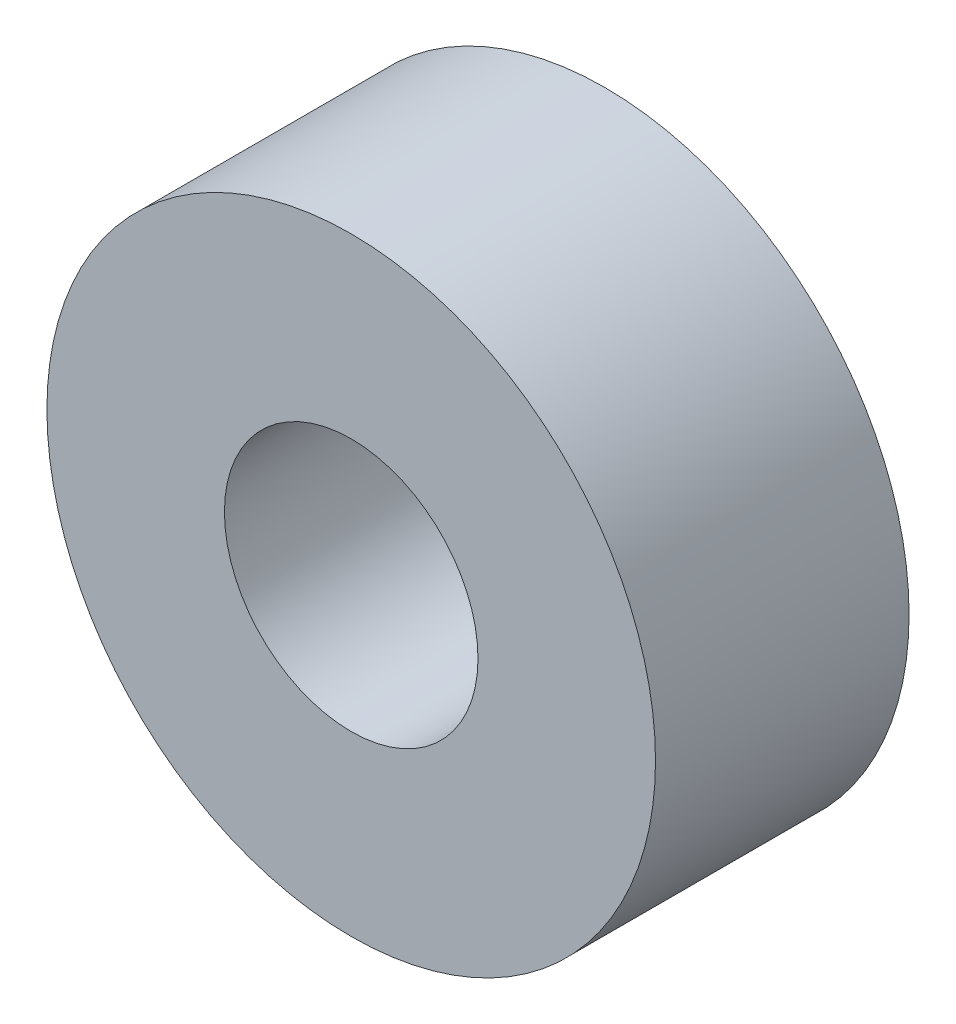
SolidWorks part; units mm, degrees
material "6061 合金"
ref_plane "前视基准面" through (0, 0, 0) normal (0, 0, 1) x (1, 0, 0)
ref_plane "上视基准面" through (0, 0, 0) normal (0, 1, 0) x (1, 0, 0)
ref_plane "右视基准面" through (0, 0, 0) normal (1, 0, 0) x (0, 0, -1)
sketch "草图1" plane through (0, 0, 0) normal (0, 0, 1) x (1, 0, 0)
  circle A0 centre (0, 0) radius 12
  circle A1 centre (0, 0) radius 5
  dimension "D1" = 24
  dimension "D2" = 10
extrude "凸台-拉伸1" add sketch "草图1" along normal mid plane 10
